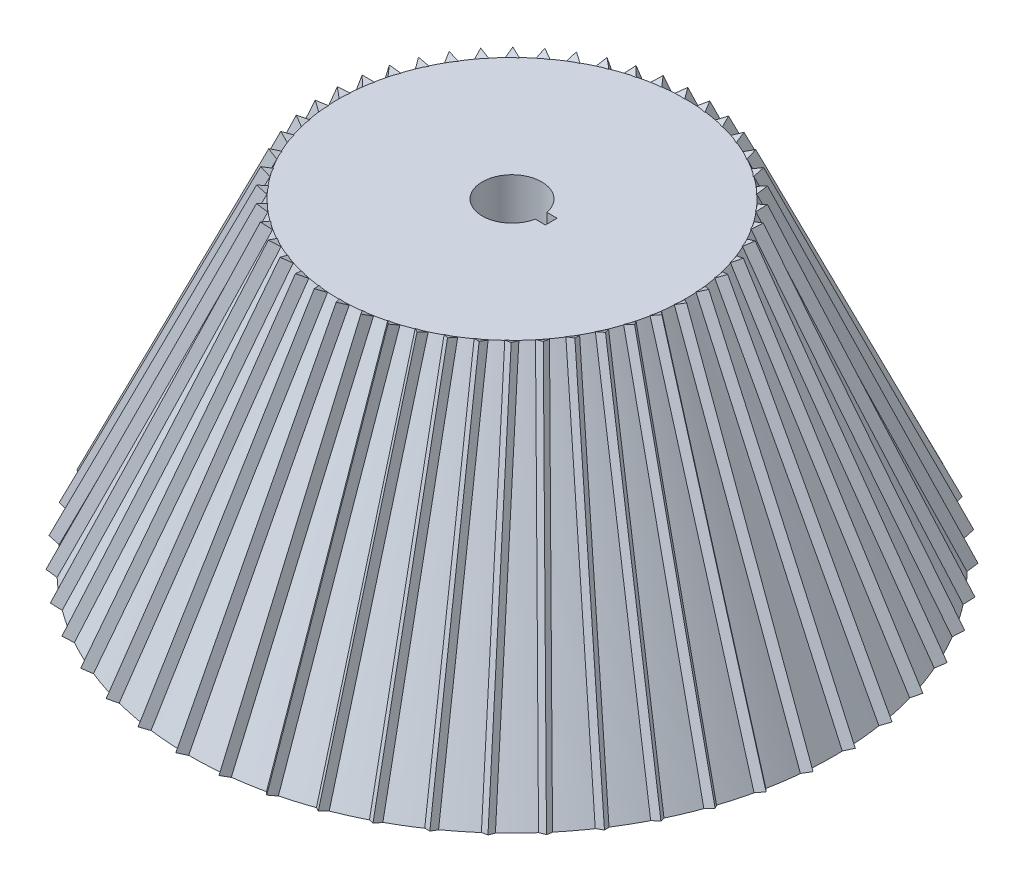
SolidWorks part; units mm, degrees
ref_plane "Front" through (0, 0, 0) normal (0, 0, 1) x (1, 0, 0)
ref_plane "Top" through (0, 0, 0) normal (0, 1, 0) x (1, 0, 0)
ref_plane "Right" through (0, 0, 0) normal (1, 0, 0) x (0, 0, -1)
sketch "Sketch1" plane through (0, 0, 0) normal (0, 0, 1) x (1, 0, 0)
  line L0 (0, 0) -> (65, 0)
  line L1 (65, 0) -> (35, 65)
  line L2 (35, 65) -> (0, 65)
  line L3 (0, 65) -> (0, 0)
  dimension "D2" = 35
  dimension "D3" = 65
revolve "Revolve1" add sketch "Sketch1" angle 360 about L3
sketch "Sketch2" plane through (0, 65, 0) normal (0, 1, 0) x (1, 0, 0)
  line L1 (5.8813, -1.1875) -> (7.9297, -1.1875)
  line L3 (5.8813, 1.1875) -> (7.9297, 1.1875)
  line L4 (7.9297, -1.1875) -> (7.9297, 1.1875)
  arc A0 (5.8813, 1.1875) -> (5.8813, -1.1875) centre (0, 0) ccw
  point P3 (6, 0)
  dimension "D1" = 12
extrude "Cut-Extrude1" cut sketch "Sketch2" against normal blind 102
sketch3d "3DSketch1"
  line L0 (34.8492, 65, -3.2456) -> (64.9415, 0, -2.757)
  circle A0 centre (0, 65, 0) radius 35 construction
  circle A1 centre (0, 0, 0) radius 65 construction
  point P0 (34.8492, 65, -3.2456)
  point P1 (64.9415, 0, -2.757)
  point P4 (0, 100, 0)
  point P8 (0, 65, 0)
ref_plane "Plane1" through (34.8492, 65, -3.2456) normal (0.4201, -0.9074, 0.0068) x (-0.9075, -0.4201, 0.0032)
sketch "Sketch3" plane through (34.8492, 65, -3.2456) normal (0.4201, -0.9074, 0.0068) x (-0.9075, -0.4201, 0.0032)
  line L1 (0.9299, 1.4612) -> (-1.7304, 0.0747)
  line L2 (-1.7304, 0.0747) -> (0.8005, -1.536)
  line L3 (0.8005, -1.536) -> (0.9299, 1.4612)
  circle A0 centre (0, 0) radius 0.866 construction
  dimension "D1" = 3
sweep "Sweep1" add profiles "Sketch3" path "3DSketch1"
pattern_circular "CirPattern1" count 50 over 360 about axis through (0, 0, 0) along (0, 1, 0) of "Sweep1"
